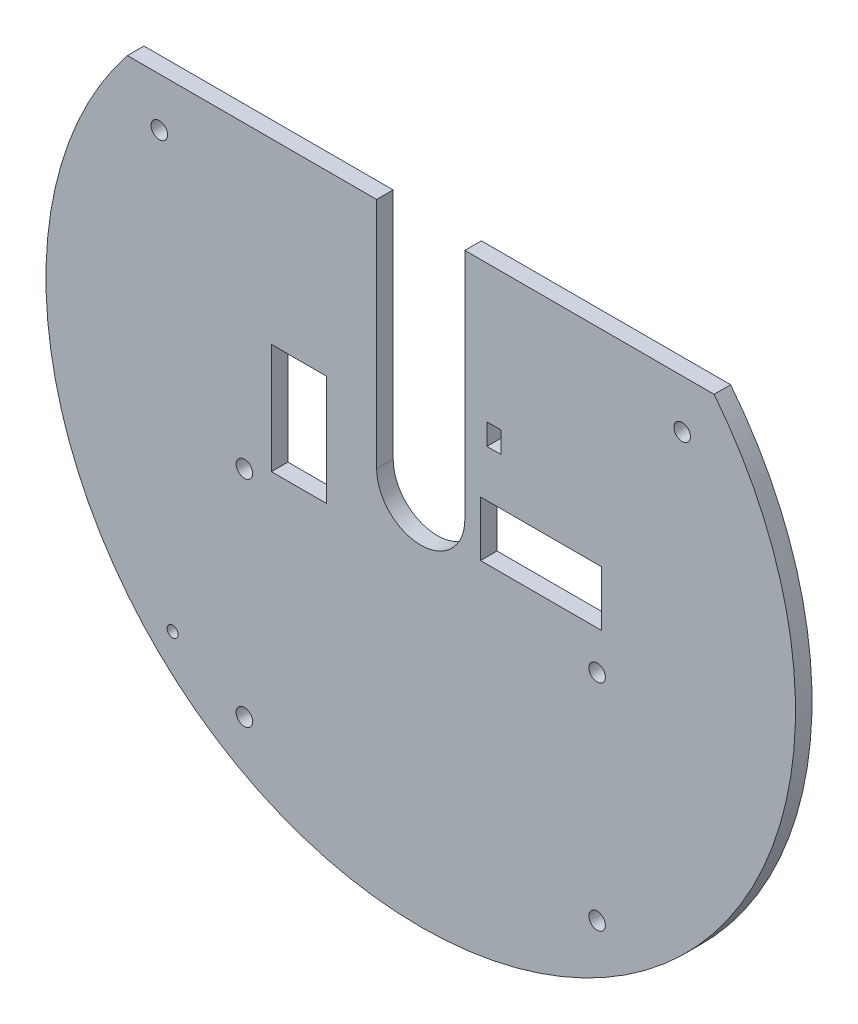
SolidWorks part; units mm, degrees
ref_plane "Front Plane" through (0, 0, 0) normal (0, 0, 1) x (1, 0, 0)
ref_plane "Top Plane" through (0, 0, 0) normal (0, 1, 0) x (1, 0, 0)
ref_plane "Right Plane" through (0, 0, 0) normal (1, 0, 0) x (0, 0, -1)
sketch "Sketch1" plane through (0, 0, 0) normal (0, 0, 1) x (1, 0, 0)
  line L0 (-47.4303, 33.5) -> (-64.0749, 33.5) construction
  line L2 (75, 0) -> (71.5, 0) construction
  line L6 (-59.9303, 23.5) -> (-41.9303, 23.5) construction
  line L13 (-59.9303, 23.5) -> (-59.9303, -23.5) construction
  line L14 (-59.9303, -23.5) -> (-41.9303, -23.5) construction
  line L15 (-41.9303, 23.5) -> (-41.9303, -23.5) construction
  line L16 (-59.9303, 23.5) -> (-41.9303, -23.5) construction
  line L17 (-59.9303, -23.5) -> (-41.9303, 23.5) construction
  line L22 (58.944, -23.1127) -> (40.944, -23.1127) construction
  line L23 (40.944, 23.8873) -> (40.944, -23.1127) construction
  line L24 (58.944, 23.8873) -> (40.944, 23.8873) construction
  line L25 (58.944, 23.8873) -> (58.944, -23.1127) construction
  line L26 (53.2269, 42.319) -> (8, 42.319)
  line L39 (0, 0) -> (0, 100.1926) construction
  line L40 (-55.4303, 39) -> (-49.4303, 39) construction
  line L41 (-10, -63.5) -> (10, -63.5) construction
  line L42 (-10, -62) -> (10, -62) construction
  line L43 (-10, -65) -> (10, -65) construction
  line L44 (-55.4303, 39) -> (-55.4303, 28) construction
  line L45 (-50.9303, 23.5) -> (-50.9303, 50.6806) construction
  line L46 (-56.5034, 49.319) -> (56.5034, 49.319) construction
  line L47 (-55.4303, 28) -> (-49.4303, 28) construction
  line L48 (-49.4303, 39) -> (-49.4303, 28) construction
  line L49 (-55.4303, 39) -> (-49.4303, 28) construction
  line L50 (-55.4303, 28) -> (-49.4303, 39) construction
  line L55 (55.4303, 39) -> (49.4303, 39) construction
  line L56 (55.4303, 28) -> (49.4303, 28) construction
  line L57 (49.4303, 39) -> (49.4303, 28) construction
  line L58 (55.4303, 39) -> (55.4303, 28) construction
  line L59 (162.9489, -263.5978) -> (-50.4314, -45.6907) construction
  line L60 (-53.5344, -35.3754) -> (-29.163, -60.2638) construction
  line L61 (40.944, -23.1127) -> (40.944, -49.5933) construction
  line L62 (-8, 0) -> (-8, 42.319)
  line L63 (34.944, -30.3857) -> (40.944, -30.3857) construction
  line L64 (34.944, -30.3857) -> (34.944, -42.3857) construction
  line L65 (34.944, -42.3857) -> (40.944, -42.3857) construction
  line L66 (40.944, -30.3857) -> (40.944, -42.3857) construction
  line L67 (34.944, -30.3857) -> (40.944, -42.3857) construction
  line L68 (34.944, -42.3857) -> (40.944, -30.3857) construction
  line L70 (8, 42.319) -> (8, 0)
  line L71 (0, 0) -> (0, -77.9694) construction
  line L73 (32.8438, 5) -> (10.8438, 5)
  line L74 (32.8438, 5) -> (32.8438, -5)
  line L75 (32.8438, -5) -> (10.8438, -5)
  line L76 (10.8438, 5) -> (10.8438, -5)
  line L77 (32.8438, 5) -> (10.8438, -5) construction
  line L78 (32.8438, -5) -> (10.8438, 5) construction
  line L82 (-8, 42.319) -> (-53.2269, 42.319)
  line L83 (-27.0947, 10) -> (-17.0947, 10)
  line L84 (-27.0947, 10) -> (-27.0947, -10)
  line L85 (-27.0947, -10) -> (-17.0947, -10)
  line L86 (-17.0947, 10) -> (-17.0947, -10)
  line L87 (-27.0947, 10) -> (-17.0947, -10) construction
  line L88 (-27.0947, -10) -> (-17.0947, 10) construction
  circle A2 centre (71.5, 0) radius 1.5 construction
  circle A4 centre (22.0947, -68.0592) radius 1.5 construction
  circle A5 centre (-22.0947, -68.0005) radius 1.5 construction
  circle A7 centre (-71.5, 0) radius 1.5 construction
  arc A13 (-53.2269, 42.319) -> (53.2269, 42.319) centre (0, 0) ccw
  arc A14 (-8, 0) -> (8, 0) centre (0, 0) ccw
  circle A16 centre (-27, 9) radius 1.5 construction
  circle A17 centre (-27, -9) radius 1.5 construction
  circle A18 centre (47.4303, 33.5) radius 1.5
  circle A19 centre (26.9209, -9) radius 1.5 construction
  circle A20 centre (26.9209, 9) radius 1.5 construction
  arc A25 (-10, -62) -> (-10, -65) centre (-10, -63.5) ccw construction
  arc A26 (10, -65) -> (10, -62) centre (10, -63.5) ccw construction
  circle A27 centre (20, 45.819) radius 1.5 construction
  circle A28 centre (-20, 45.819) radius 1.5 construction
  circle A29 centre (-47.4303, 33.5) radius 1.5
  arc A32 (-56.5034, 49.319) -> (56.5034, 49.319) centre (0, 0) ccw construction
  circle A33 centre (-32.4192, -56.9385) radius 1 construction
  circle A34 centre (-45.0128, -44.0777) radius 1
  circle A35 centre (37.944, -28.3857) radius 1 construction
  circle A36 centre (37.944, -44.3857) radius 1 construction
  circle A37 centre (-32, -12) radius 1.5
  circle A38 centre (-32, -51) radius 1.5
  circle A39 centre (32, -51) radius 1.5
  circle A40 centre (32, -12) radius 1.5
  point P7 (-52.4303, 33.5)
  point P8 (21.8438, 0)
  point P24 (0, 0)
  point P26 (0, 0)
  point P34 (-50.9303, 0)
  point P63 (0, 0)
  point P65 (0, -63.5)
  point P76 (37.944, -36.3857)
  point P96 (-22.0947, 0)
  dimension "D3" = 3
  dimension "D5" = 150
  dimension "D6" = 16
  dimension "D7" = 7
  dimension "D13" = 3
  dimension "D14" = 2
  dimension "D16" = 2
  dimension "D19" = 1.5
  dimension "D21" = 3
  dimension "D23" = 3
  dimension "D26" = 3.5
  dimension "D8" = 7
  dimension "D15" = 2
  dimension "D17" = 5
  dimension "D27" = 3
  dimension "D28" = 2
  dimension "D29" = 2
  dimension "D34" = 2
  dimension "D37" = 16
  dimension "D38" = 47
  dimension "D40" = 12
  dimension "D41" = 3
  dimension "D42" = 3
  dimension "D2" = 3.5
  dimension "D9" = 6
  dimension "D10" = 11
  dimension "D11" = 18
  dimension "D12" = 47
  dimension "D18" = 20
  dimension "D20" = 65
  dimension "D22" = 18
  dimension "D24" = 10
  dimension "D25" = 3.5
  dimension "D4" = 3.5
  dimension "D30" = 16
  dimension "D31" = 12
  dimension "D32" = 6
  dimension "D33" = 3
  dimension "D35" = 20
  dimension "D36" = 20
  dimension "D39" = 32
  dimension "D43" = 39
  dimension "D44" = 10
  dimension "D45" = 22
  dimension "D46" = 10
  dimension "D47" = 20
extrude "Boss-Extrude2" add sketch "Sketch1" along normal blind 3
sketch "Sketch2" plane through (0, 0, 3) normal (0, 0, 1) x (1, 0, 0)
  line L0 (53.2269, 42.319) -> (8, 42.319) construction
  line L1 (12, 13.519) -> (14.6, 13.519) construction
  line L2 (12, 13.519) -> (12, 9.719) construction
  line L3 (12, 9.719) -> (14.6, 9.719) construction
  line L4 (14.6, 13.519) -> (14.6, 9.719) construction
  line L5 (12, 13.519) -> (14.6, 9.719) construction
  line L6 (12, 9.719) -> (14.6, 13.519) construction
  line L7 (8, 42.319) -> (8, 0) construction
  line L8 (12, 17.3802) -> (14.6, 17.3802)
  line L9 (12, 17.3802) -> (12, 13.519)
  line L10 (12, 13.519) -> (14.6, 13.519)
  line L11 (14.6, 17.3802) -> (14.6, 13.519)
  point P0 (13.3, 11.619)
  point P13 (0, 0)
  point P14 (0, 0)
  dimension "D1" = 3.8
  dimension "D2" = 2.6
  dimension "D3" = 28.8
  dimension "D4" = 4
extrude "Cut-Extrude1" cut sketch "Sketch2" against normal blind 3
